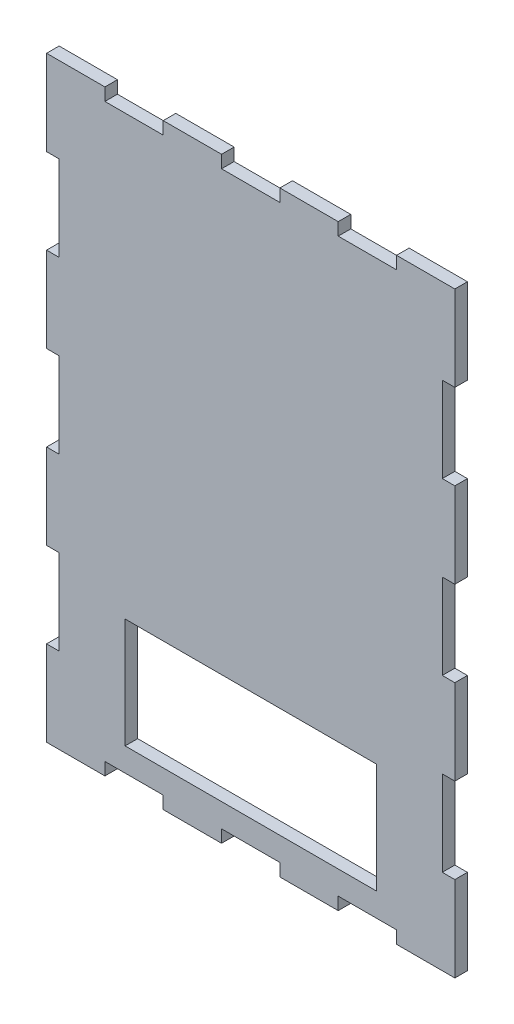
SolidWorks part; units mm, degrees
ref_plane "Front Plane" through (0, 0, 0) normal (0, 0, 1) x (1, 0, 0)
ref_plane "Top Plane" through (0, 0, 0) normal (0, 1, 0) x (1, 0, 0)
ref_plane "Right Plane" through (0, 0, 0) normal (1, 0, 0) x (0, 0, -1)
sketch "Buitenafmeting Rechthoek" plane through (0, 0, 0) normal (0, 0, 1) x (1, 0, 0)
  line L1 (0, 0) -> (130, 0)
  line L2 (0, 0) -> (0, 190)
  line L3 (0, 190) -> (130, 190)
  line L4 (130, 0) -> (130, 190)
  dimension "D1" = 130
  dimension "D2" = 190
extrude "Plaat" add sketch "Buitenafmeting Rechthoek" against normal blind 4
sketch "Tand Hor" plane through (0, 0, 0) normal (0, 0, 1) x (1, 0, 0)
  line L1 (130, 190) -> (0, 190) construction
  line L2 (18.5714, 190) -> (37.1429, 190)
  line L3 (18.5714, 190) -> (18.5714, 186)
  line L4 (18.5714, 186) -> (37.1429, 186)
  line L6 (37.1429, 190) -> (37.1429, 186)
  dimension "D1" = 4
  dimension "D2" = 18.5714
  dimension "D3" = 18.5714
extrude "Tand Boven" cut sketch "Tand Hor" against normal through all
pattern_linear "Tanden Patroon Boven" count 3 spacing 37.1429 along (1, 0, 0) of "Tand Boven"
sketch "Tand Ver" plane through (0, 0, 0) normal (0, 0, 1) x (1, 0, 0)
  line L0 (0, 190) -> (0, 0) construction
  line L1 (0, 162.8571) -> (4, 162.8571)
  line L2 (0, 162.8571) -> (0, 135.7143)
  line L3 (0, 135.7143) -> (4, 135.7143)
  line L4 (4, 162.8571) -> (4, 135.7143)
  dimension "D1" = 4
  dimension "D2" = 27.1429
  dimension "D3" = 162.8571
extrude "Tand Links" cut sketch "Tand Ver" against normal through all
pattern_linear "Tanden Patroon Links" count 3 spacing 54.2857 along (0, -1, 0) of "Tand Links"
sketch "Tand O" plane through (0, 0, 0) normal (0, 0, 1) x (1, 0, 0)
  line L0 (0, 0) -> (130, 0) construction
  line L1 (18.5714, 0) -> (37.1429, 0)
  line L2 (18.5714, 0) -> (18.5714, 4)
  line L3 (18.5714, 4) -> (37.1429, 4)
  line L4 (37.1429, 0) -> (37.1429, 4)
  dimension "D1" = 4
  dimension "D2" = 18.5714
  dimension "D3" = 18.5714
extrude "Tand Onder" cut sketch "Tand O" against normal through all
pattern_linear "Tanden Patroon Onder" count 3 spacing 37.1429 along (1, 0, 0) of "Tand Onder"
sketch "Tand R" plane through (0, 0, 0) normal (0, 0, 1) x (1, 0, 0)
  line L0 (130, 0) -> (130, 190) construction
  line L1 (130, 162.8571) -> (126, 162.8571)
  line L2 (130, 162.8571) -> (130, 135.7143)
  line L3 (130, 135.7143) -> (126, 135.7143)
  line L4 (126, 162.8571) -> (126, 135.7143)
  dimension "D1" = 4
  dimension "D2" = 27.1429
  dimension "D3" = 162.8571
extrude "Tand Rechts" cut sketch "Tand R" against normal through all
pattern_linear "Tanden Patroon Rechts" count 3 spacing 54.2857 along (0, -1, 0) of "Tand Rechts"
sketch "Sketch1" plane through (0, 0, 0) normal (0, 0, 1) x (1, 0, 0)
  line L0 (126, 54.2857) -> (126, 27.1429) construction
  line L1 (25, 46.5) -> (105, 46.5)
  line L2 (25, 46.5) -> (25, 11.5)
  line L3 (25, 11.5) -> (105, 11.5)
  line L4 (105, 46.5) -> (105, 11.5)
  line L5 (4, 27.1429) -> (4, 54.2857) construction
  line L6 (74.2857, 4) -> (55.7143, 4) construction
  dimension "D1" = 80
  dimension "D2" = 35
  dimension "D3" = 21
  dimension "D4" = 21
  dimension "D5" = 7.5
extrude "Cut-Extrude1" cut sketch "Sketch1" against normal blind 10
equation "\"D1@Buitenafmeting Rechthoek\"= \"Lengte\""
equation "\"D2@Buitenafmeting Rechthoek\" = \"Hoogte\""
equation "\"D1@Plaat\" = \"Dikte\""
equation "\"D3@Tanden Patroon Boven\" = \"LengteHorTand\" * 2"
equation "\"D1@Tanden Patroon Boven\" = \"nPatroonHor\""
equation "\"LengteHorTand\"= \"Lengte\" / \"nHor\"'Spatie tussen verschillende tanden in de lengte"
equation "\"nPatroonHor\"= ( \"nHor\" + 1 ) / 2 - \"GrensHor\"'Aantal kopies van tanden in de lengte"
equation "\"D1@Tand Hor\" = \"Dikte\""
equation "\"D2@Tand Hor\" = \"LengteHorTand\""
equation "\"D1@Tand Ver\" = \"Dikte\""
equation "\"LengteVertTand\"= \"Hoogte\" / \"nVert\"'Spatie tussen verschillende tanden in de hoogte"
equation "\"nPatroonVert\"= ( \"nVert\" + 1 ) / 2 - \"GrensVert\"'Aantal kopies van tanden in de hoogte"
equation "\"D2@Tand Ver\"=\"LengteVertTand\""
equation "\"D3@Tanden Patroon Links\"=\"LengteVertTand\"*2"
equation "\"D3@Tanden Patroon Rechts\"=\"LengteVertTand\"*2"
equation "\"D1@Tanden Patroon Rechts\"=\"nPatroonVert\""
equation "\"D3@Tanden Patroon Onder\"=\"LengteHorTand\"*2"
equation "\"D1@Tanden Patroon Onder\"=\"nPatroonHor\""
equation "\"D1@Tanden Patroon Links\"=\"nPatroonVert\""
equation "\"D3@Tand Ver\"=\"Hoogte\"-\"GrensVert\"*\"LengteVertTand\""
equation "\"D2@Tand R\" = \"LengteVertTand\""
equation "\"D3@Tand R\" = \"Hoogte\" - \"GrensVert\" * \"LengteVertTand\""
equation "\"D2@Tand O\"=\"LengteHorTand\""
equation "\"D3@Tand Hor\"=\"GrensHor\"*\"LengteHorTand\""
equation "\"D3@Tand O\"=\"GrensHor\"*\"LengteHorTand\""
equation "\"Tand Boven\"= IIF ( \"plaatsTandenBoven\" , \"unsuppressed\" , \"suppressed\" )"
equation "\"Tanden Patroon Boven\"= IIF ( \"plaatsTandenBoven\" , \"unsuppressed\" , \"suppressed\" )"
equation "\"Tand Links\"= IIF ( \"plaatsTandenLinks\" , \"unsuppressed\" , \"suppressed\" )"
equation "\"Tanden Patroon Links\"= IIF ( \"plaatsTandenLinks\" , \"unsuppressed\" , \"suppressed\" )"
equation "\"Tand Onder\"= IIF ( \"plaatsTandenOnder\" , \"unsuppressed\" , \"suppressed\" )"
equation "\"Tanden Patroon Onder\"= IIF ( \"plaatsTandenOnder\" , \"unsuppressed\" , \"suppressed\" )"
equation "\"Tand Rechts\"= IIF ( \"plaatsTandenRechts\" , \"unsuppressed\" , \"suppressed\" )"
equation "\"Tanden Patroon Rechts\"= IIF ( \"plaatsTandenRechts\" , \"unsuppressed\" , \"suppressed\" )"
equation "\"D1@Tand O\"=\"Dikte\""
equation "\"D1@Tand R\"=\"Dikte\""
